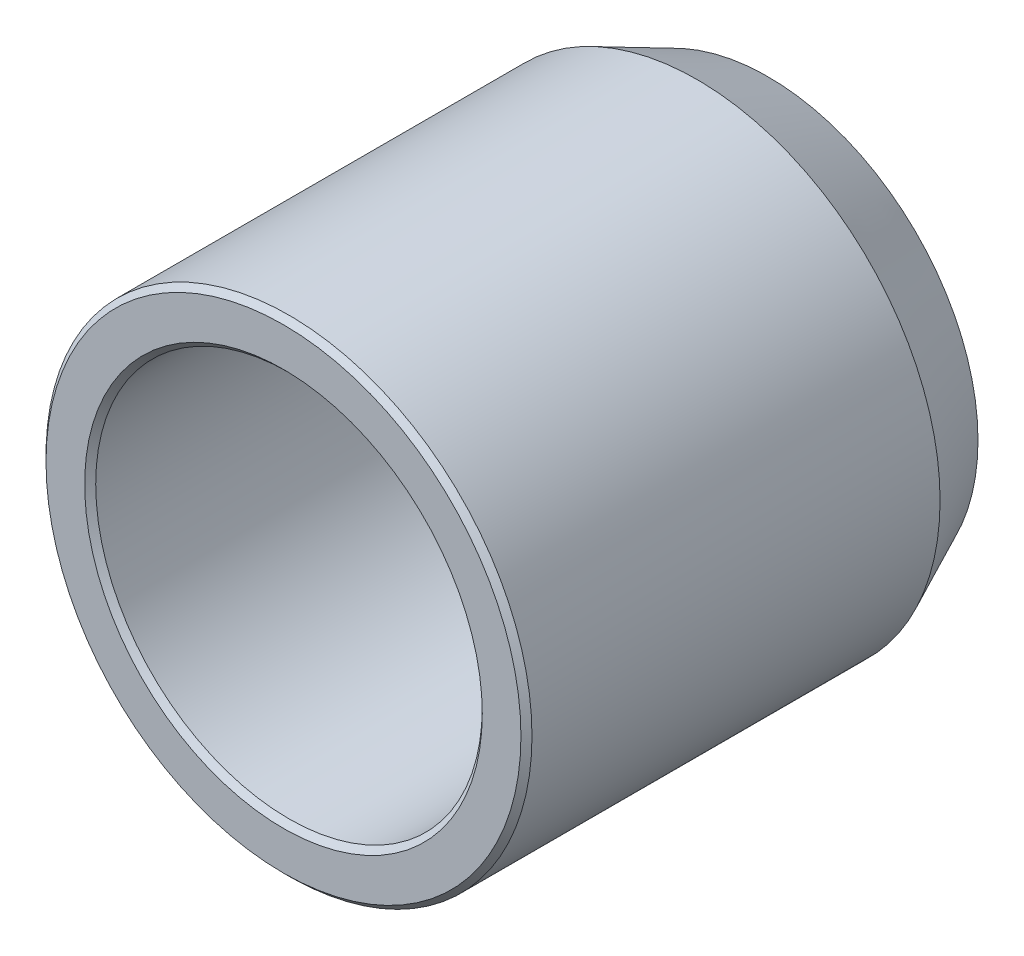
SolidWorks part; units mm, degrees
material "1023 Arkusz stali węglowej (SS)"
ref_plane "Płaszczyzna przednia" through (0, 0, 0) normal (0, 0, 1) x (1, 0, 0)
ref_plane "Płaszczyzna górna" through (0, 0, 0) normal (0, 1, 0) x (1, 0, 0)
ref_plane "Płaszczyzna prawa" through (0, 0, 0) normal (1, 0, 0) x (0, 0, -1)
sketch "Szkic2" plane through (0, 0, 0) normal (1, 0, 0) x (0, 0, -1)
  line L0 (0, 0) -> (55.8908, 0) construction
  line L1 (0, 18) -> (0, 21.5)
  line L2 (0.5, 17.5) -> (38.88, 17.5)
  line L3 (43.88, 16) -> (43.88, 19)
  line L4 (0.5, 22) -> (37.4465, 22)
  line L5 (37.4465, 22) -> (43.88, 19)
  line L6 (38.88, 17.5) -> (38.88, 16.5)
  line L7 (39.38, 16) -> (43.88, 16)
  line L8 (38.88, 16.5) -> (39.38, 16)
  line L9 (0.5, 17.5) -> (0, 18)
  line L10 (0, 21.5) -> (0.5, 22)
  point P3 (0, 17.5)
  point P4 (0, 22)
  point P9 (38.88, 16)
  dimension "D1" = 35
  dimension "D2" = 38
  dimension "D3" = 44
  dimension "D4" = 43.88
  dimension "D5" = 115
  dimension "D6" = 32
  dimension "D7" = 5
revolve "Obrót1" add sketch "Szkic2" angle 360 about L0
